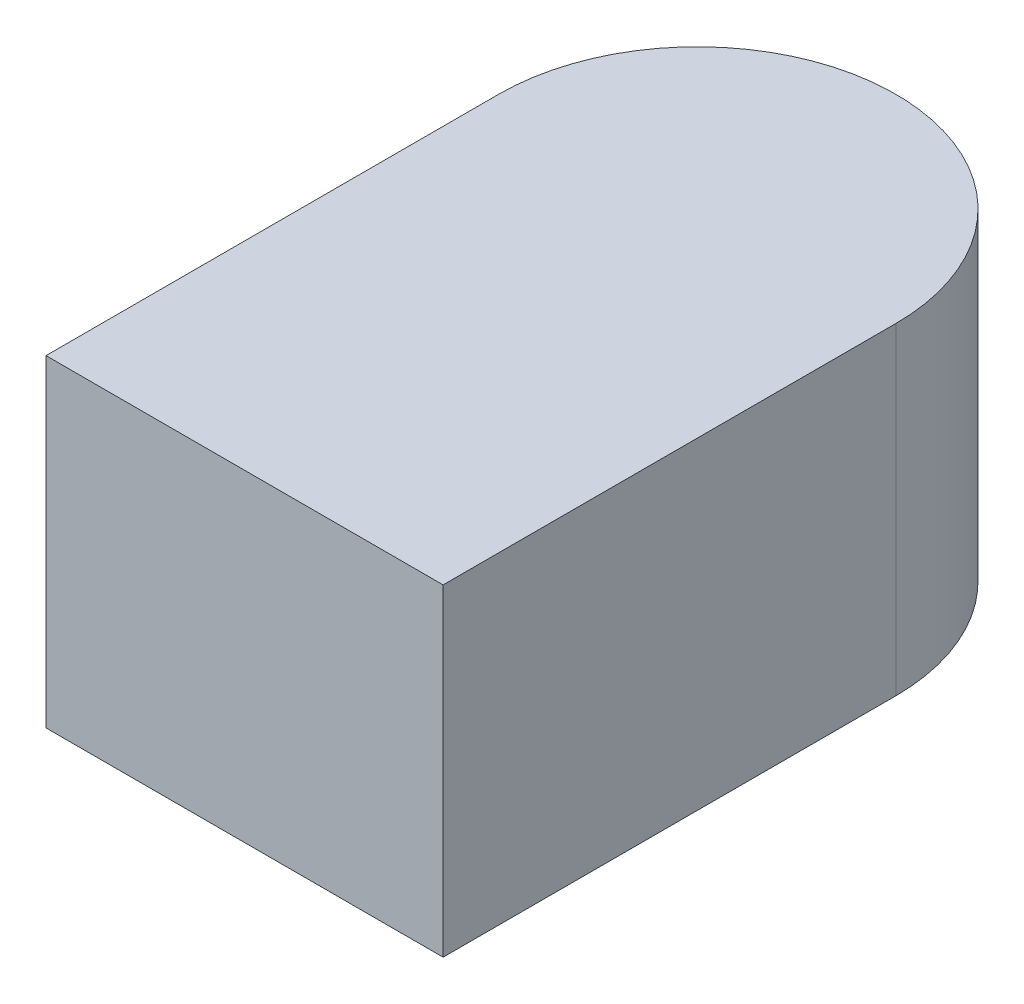
SolidWorks part; units mm, degrees
material "1060-H16"
ref_plane "Front Plane" through (0, 0, 0) normal (0, 0, 1) x (1, 0, 0)
ref_plane "Top Plane" through (0, 0, 0) normal (0, 1, 0) x (1, 0, 0)
ref_plane "Right Plane" through (0, 0, 0) normal (1, 0, 0) x (0, 0, -1)
sketch "Sketch1" plane through (0, 0, 0) normal (0, 1, 0) x (1, 0, 0)
  line L1 (-0.125, 0.1425) -> (0.125, 0.1425) construction
  line L2 (-0.125, 0.1425) -> (-0.125, -0.1425)
  line L3 (-0.125, -0.1425) -> (0.125, -0.1425)
  line L4 (0.125, 0.1425) -> (0.125, -0.1425)
  line L5 (-0.125, 0.1425) -> (0.125, -0.1425) construction
  line L6 (-0.125, -0.1425) -> (0.125, 0.1425) construction
  arc A0 (0.125, 0.1425) -> (-0.125, 0.1425) centre (0, 0.1425) ccw
  point P0 (0, 0)
  point P7 (0, 0.2675)
  dimension "D1" = 0.25
  dimension "D2" = 0.41
extrude "Boss-Extrude1" add sketch "Sketch1" along normal blind 0.203
